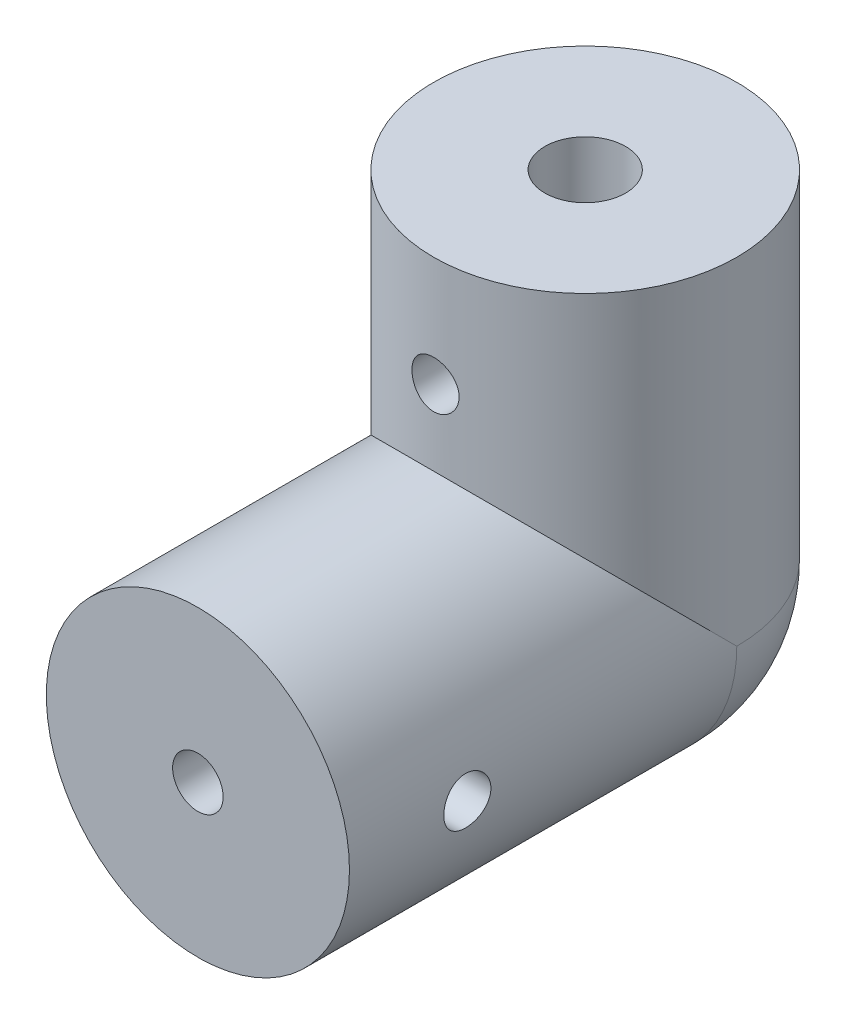
SolidWorks part; units mm, degrees
ref_plane "Alzado" through (0, 0, 0) normal (0, 0, 1) x (1, 0, 0)
ref_plane "Planta" through (0, 0, 0) normal (0, 1, 0) x (1, 0, 0)
ref_plane "Vista lateral" through (0, 0, 0) normal (1, 0, 0) x (0, 0, -1)
sketch "Croquis1" plane through (0, 0, 0) normal (0, 0, 1) x (1, 0, 0)
  circle A0 centre (0, 0) radius 9
  circle A1 centre (0, 0) radius 1.5
  dimension "D1" = 18
  dimension "D2" = 3
extrude "Saliente-Extruir1" add sketch "Croquis1" along normal blind 15 and the other way blind 8
sketch "Croquis2" plane through (0, 0, 0) normal (0, 1, 0) x (1, 0, 0)
  circle A1 centre (0, 8) radius 2.4
  circle A2 centre (0, 8) radius 9
  dimension "D1" = 18
  dimension "D2" = 4.8
  dimension "D3" = 8
extrude "Saliente-Extruir4" add sketch "Croquis2" along normal blind 20
sketch "Croquis6" plane through (0, 0, -8) normal (0, 0, -1) x (-1, 0, 0)
  line L0 (0, 0) -> (0, -9)
  line L1 (0, 0) -> (-9, 0)
  arc A0 (-9, 0) -> (9, 0) centre (0, 0) ccw construction
  arc A1 (-9, 0) -> (0, -9) centre (0, 0) ccw
revolve "Revolución4" add sketch "Croquis6" angle 360 about L0
sketch "Croquis7" plane through (0, 20, 0) normal (0, 1, 0) x (1, 0, 0)
  circle A0 centre (0, 8) radius 2.4
  dimension "D1" = 4.8
extrude "Cortar-Extruir1" cut sketch "Croquis7" against normal blind 20
sketch "Croquis8" plane through (0, 0, 15) normal (0, 0, 1) x (1, 0, 0)
  circle A0 centre (0, 0) radius 1.5
  dimension "D1" = 3
extrude "Cortar-Extruir2" cut sketch "Croquis8" against normal blind 15
ref_plane "Plano1" through (-9, 0, 0) normal (-1, 0, 0) x (0, 0, 1)
sketch "Croquis9" plane through (-9, 0, 0) normal (-1, 0, 0) x (0, 0, 1)
  line L0 (8, 9) -> (8, -9) construction
  line L1 (15, 9) -> (1, 9) construction
  line L2 (-8, -9) -> (15, -9) construction
  circle A0 centre (8, 0) radius 1.4
  dimension "D1" = 2.8
extrude "Cortar-Extruir3" cut sketch "Croquis9" against normal through all
ref_plane "Plano2" through (0, 0, -17) normal (0, 0, -1) x (-1, 0, 0)
sketch "Croquis10" plane through (0, 0, -17) normal (0, 0, -1) x (-1, 0, 0)
  line L0 (9, 13.459) -> (-9, 13.459) construction
  line L1 (9, 0) -> (9, 20) construction
  line L2 (-9, 20) -> (-9, 0) construction
  circle A0 centre (0, 13.459) radius 1.4
  dimension "D1" = 2.8
extrude "Cortar-Extruir4" cut sketch "Croquis10" against normal through all and the other way through all
